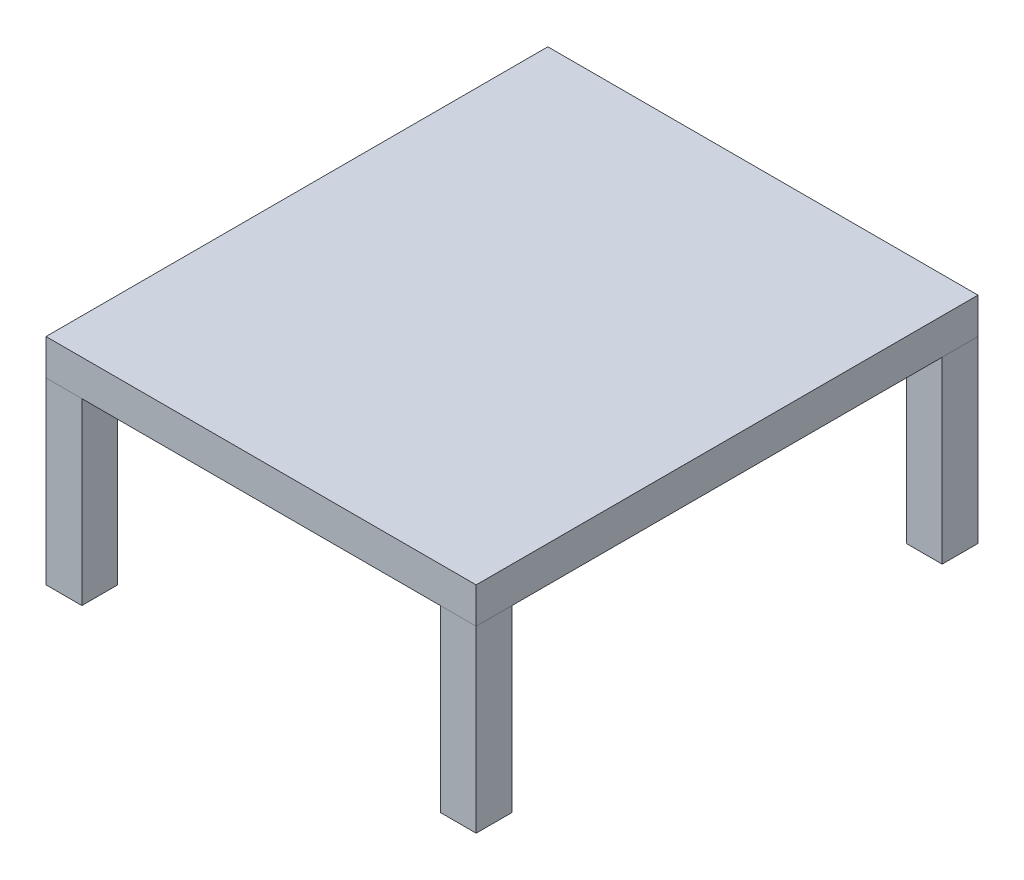
SolidWorks part; units mm, degrees
ref_plane "Front Plane" through (0, 0, 0) normal (0, 0, 1) x (1, 0, 0)
ref_plane "Top Plane" through (0, 0, 0) normal (0, 1, 0) x (1, 0, 0)
ref_plane "Right Plane" through (0, 0, 0) normal (1, 0, 0) x (0, 0, -1)
sketch "Sketch1" plane through (0, 0, 0) normal (0, 1, 0) x (1, 0, 0)
  line L0 (0, 0) -> (0, 333.6192) construction
  line L1 (-304.8, 355.6) -> (-254, 355.6)
  line L2 (-304.8, 355.6) -> (-304.8, 304.8)
  line L3 (-304.8, 304.8) -> (-254, 304.8)
  line L4 (-254, 355.6) -> (-254, 304.8)
  line L5 (0, 0) -> (-385.8541, 0) construction
  line L14 (-254, -355.6) -> (-254, -304.8)
  line L15 (-304.8, -304.8) -> (-254, -304.8)
  line L16 (-304.8, -355.6) -> (-304.8, -304.8)
  line L17 (-304.8, -355.6) -> (-254, -355.6)
  point P10 (-284.5842, 0)
  dimension "D1" = 50.8
  dimension "D3" = 609.6
extrude "Boss-Extrude1" add sketch "Sketch1" along normal blind 254
mirror "Mirror4" about plane through (0, 0, 0) normal (1, 0, 0) of bodies 101 104
sketch "Sketch2" plane through (0, 254, 0) normal (0, 1, 0) x (1, 0, 0)
  line L1 (-304.8, -355.6) -> (304.8, -355.6)
  line L2 (-304.8, -355.6) -> (-304.8, 355.6)
  line L3 (-304.8, 355.6) -> (304.8, 355.6)
  line L4 (304.8, -355.6) -> (304.8, 355.6)
extrude "Boss-Extrude2" add sketch "Sketch2" along normal blind 50.8 separate body
